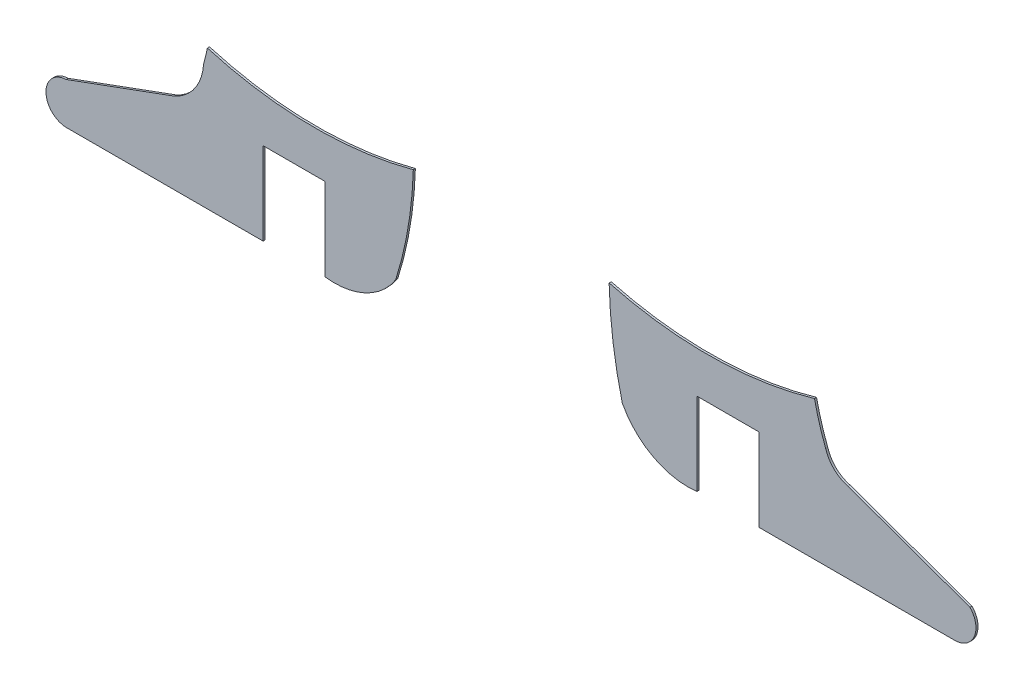
SolidWorks part; units mm, degrees
ref_plane "Alzado" through (0, 0, 0) normal (0, 0, 1) x (1, 0, 0)
ref_plane "Planta" through (0, 0, 0) normal (0, 1, 0) x (1, 0, 0)
ref_plane "Vista lateral" through (0, 0, 0) normal (1, 0, 0) x (0, 0, -1)
sketch "Model" plane through (0, 0, 0) normal (0, 0, 1) x (1, 0, 0)
  line L0 (48.0049, 11.4811) -> (48.0001, 15.4802)
  line L1 (48.0001, 15.4802) -> (45.0043, 15.4797)
  line L2 (45.0043, 15.4797) -> (45.0049, 11.4797)
  line L3 (45.0049, 11.4797) -> (35.5062, 11.4784)
  line L4 (35.463, 13.4857) -> (40.6651, 15.3944)
  line L5 (73.3211, 15.3575) -> (79.2204, 13.2367)
  line L6 (78.5371, 11.4819) -> (69.0001, 11.4815)
  line L7 (69.0001, 11.4815) -> (69.0001, 15.4815)
  line L8 (69.0001, 15.4815) -> (66.0001, 15.4815)
  line L9 (66.0001, 15.4815) -> (66.0001, 11.4815)
  arc A0 (48.0049, 11.4811) -> (51.4198, 13.0671) centre (48.4657, 14.9585) ccw
  arc A1 (35.463, 13.4857) -> (35.5062, 11.4784) centre (35.4961, 12.4823) ccw
  arc A2 (40.6651, 15.3944) -> (42.1204, 17.4593) centre (39.7291, 17.5994) ccw
  arc A3 (42.1204, 17.4593) -> (42.3047, 18.2256) centre (29.3407, 20.9378) ccw
  arc A4 (42.3047, 18.2256) -> (52.2728, 18.1081) centre (47.4989, 35.9815) ccw
  arc A5 (51.4198, 13.0671) -> (52.2728, 18.1081) centre (33.7594, 18.6479) ccw
  arc A6 (72.2341, 16.3982) -> (73.3211, 15.3575) centre (73.7022, 16.8434) ccw
  arc A7 (78.5371, 11.4819) -> (79.2204, 13.2367) centre (78.4684, 12.5191) ccw
  arc A8 (62.3892, 13.3804) -> (66.0001, 11.4815) centre (65.5741, 15.0542) ccw
  arc A9 (61.7512, 18.1017) -> (62.3892, 13.3804) centre (83.1722, 18.5926) ccw
  arc A10 (61.7512, 18.1017) -> (71.6914, 18.2244) centre (66.5014, 35.9815) ccw
  arc A11 (71.6914, 18.2244) -> (72.2341, 16.3982) centre (83.869, 20.8495) ccw
extrude "Saliente-Extruir1" add sketch "Model" along normal blind 0.1
